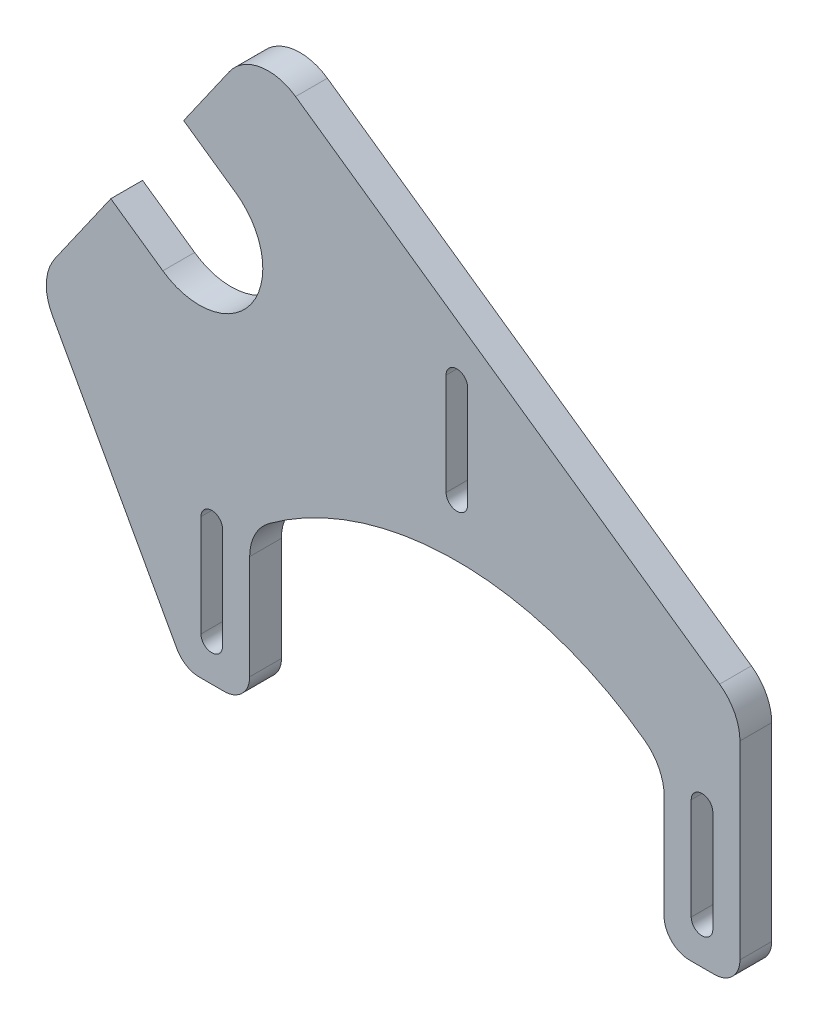
SolidWorks part; units mm, degrees
ref_plane "Front" through (0, 0, 0) normal (0, 0, 1) x (1, 0, 0)
ref_plane "Top" through (0, 0, 0) normal (0, 1, 0) x (1, 0, 0)
ref_plane "Right" through (0, 0, 0) normal (1, 0, 0) x (0, 0, -1)
sketch "Sketch1" plane through (0, 0, 0) normal (0, 0, 1) x (1, 0, 0)
  line L0 (-46.5, 0) -> (-46.5, -31.205) construction
  line L1 (-41.42, 12.7) -> (-41.42, -12.7)
  line L2 (46.5, 0) -> (46.5, -31.205) construction
  line L3 (-46.5, 0) -> (46.5, 0) construction
  line L4 (41.42, -12.7) -> (41.42, 12.7)
  line L5 (0, 61.7) -> (0, 36.3) construction
  line L6 (-54.6116, 76.999) -> (-44.2083, 69.7146)
  line L7 (-58.7772, 48.9081) -> (-69.1804, 56.1926)
  line L8 (-69.1804, 56.1926) -> (-54.6116, 76.999) construction
  line L9 (-46.5, -17.78) -> (-51.5, -17.78)
  line L10 (-83.7492, 35.3861) -> (-69.1804, 56.1926)
  line L11 (-54.6116, 76.999) -> (-40.0427, 97.8055)
  line L12 (-106.3912, -19.0917) -> (3.4057, 137.7145) construction
  line L13 (56.58, -12.7) -> (56.58, 30.1495)
  line L14 (-59.5056, 47.8678) -> (-43.4799, 70.7549) construction
  line L15 (46.5, -17.78) -> (51.5, -17.78)
  line L18 (51.5, -17.78) -> (51.5, 0) construction
  line L19 (-40.0427, 97.8055) -> (56.58, 30.1495)
  line L20 (-51.5, 0) -> (-51.5, -17.78) construction
  line L21 (-55.951, -15.1484) -> (-83.7492, 35.3861)
  circle A0 centre (49, 0) radius 2.5 construction
  arc A1 (51.5, -17.78) -> (56.58, -12.7) centre (51.5, -12.7) ccw
  arc A2 (-41.42, 12.7) -> (41.42, 12.7) centre (0, -35.4314) cw
  arc A4 (-51.5, -17.78) -> (-55.951, -15.1484) centre (-51.5, -12.7) cw
  circle A6 centre (49, 0) radius 2.5 construction
  circle A7 centre (-49, 0) radius 2.5 construction
  arc A8 (39.8609, -39.3333) -> (-39.8609, -39.3333) centre (0, 0) ccw construction
  circle A11 centre (0, 49) radius 2.5 construction
  circle A12 centre (-51.4928, 59.3114) radius 12.7 construction
  arc A15 (-44.2083, 69.7146) -> (-58.7772, 48.9081) centre (-51.4928, 59.3114) cw
  arc A16 (-41.42, -12.7) -> (-46.5, -17.78) centre (-46.5, -12.7) cw
  arc A18 (41.42, -12.7) -> (46.5, -17.78) centre (46.5, -12.7) ccw
  point P3 (-49, 0)
  point P16 (-41.42, 0)
  point P19 (41.42, 0)
  point P23 (0, 49)
  dimension "D1" = 5.08
  dimension "D4" = 5.08
  dimension "D6" = 63.5
  dimension "D2" = 5.08
  dimension "D3" = 25.4
  dimension "D5" = 25.4
extrude "Extrude1" add sketch "Sketch1" along normal blind 6.35
sketch "Sketch4" plane through (0, 0, 6.35) normal (0, 0, 1) x (1, 0, 0)
  line L0 (-51.159, -10.16) -> (-51.159, 10.16)
  line L1 (-46.841, -10.16) -> (-46.841, 10.16)
  line L2 (-51.159, 0) -> (-46.841, 0) construction
  line L3 (2.159, 38.84) -> (2.159, 59.16)
  line L4 (-2.159, 38.84) -> (-2.159, 59.16)
  line L5 (2.159, 49) -> (-2.159, 49) construction
  line L6 (51.159, -10.16) -> (51.159, 10.16)
  line L7 (46.841, -10.16) -> (46.841, 10.16)
  line L8 (46.841, 0) -> (51.159, 0) construction
  line L9 (-51.4928, 59.3114) -> (0, -36) construction
  line L10 (-51.4928, 59.3114) -> (-34.6579, 83.354) construction
  line L11 (-59.5056, 47.8678) -> (-43.4799, 70.7549) construction
  circle A0 centre (0, 49) radius 2.159 construction
  circle A1 centre (49, 0) radius 2.159 construction
  circle A2 centre (-49, 0) radius 2.159 construction
  circle A3 centre (-49, 0) radius 2.5 construction
  circle A4 centre (0, 49) radius 2.5 construction
  arc A5 (-51.159, 10.16) -> (-46.841, 10.16) centre (-49, 10.16) cw
  circle A6 centre (49, 0) radius 2.5 construction
  arc A7 (-51.159, -10.16) -> (-46.841, -10.16) centre (-49, -10.16) ccw
  arc A8 (-2.159, 59.16) -> (2.159, 59.16) centre (0, 59.16) cw
  arc A9 (-2.159, 38.84) -> (2.159, 38.84) centre (0, 38.84) ccw
  arc A10 (46.841, 10.16) -> (51.159, 10.16) centre (49, 10.16) cw
  arc A11 (46.841, -10.16) -> (51.159, -10.16) centre (49, -10.16) ccw
  circle A12 centre (0, -36) radius 6.35 construction
  arc A13 (-58.7772, 48.9081) -> (-44.2083, 69.7146) centre (-51.4928, 59.3114) ccw construction
  dimension "D1" = 4.318
  dimension "D2" = 116.619
  dimension "D3" = 20.32
extrude "Cut-Extrude3" cut sketch "Sketch4" against normal up to next
fillet "Fillet1" radius 9.525 5 edges at (56.58, 30.1495, 3.175) (41.42, 12.7, 3.175) (-41.42, 12.7, 3.175) (-83.7492, 35.3861, 3.175) (-40.0427, 97.8055, 3.175)
